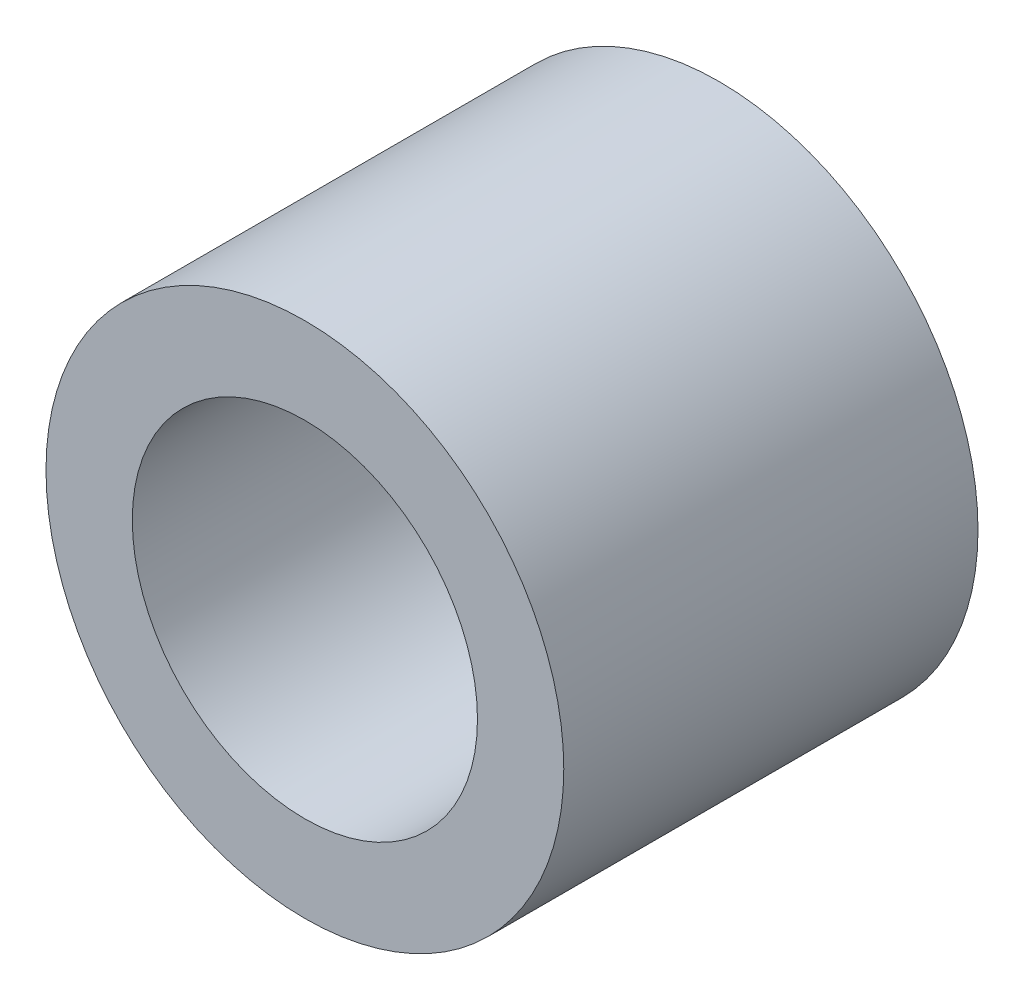
SolidWorks part; units mm, degrees
ref_plane "Front Plane" through (0, 0, 0) normal (0, 0, 1) x (1, 0, 0)
ref_plane "Top Plane" through (0, 0, 0) normal (0, 1, 0) x (1, 0, 0)
ref_plane "Right Plane" through (0, 0, 0) normal (1, 0, 0) x (0, 0, -1)
sketch "Sketch1" plane through (0, 0, 0) normal (0, 0, 1) x (1, 0, 0)
  circle A0 centre (0, 0) radius 6.35
  circle A1 centre (0, 0) radius 9.525
  dimension "D1" = 12.7
  dimension "D2" = 19.05
extrude "Boss-Extrude1" add sketch "Sketch1" along normal blind 15.24
